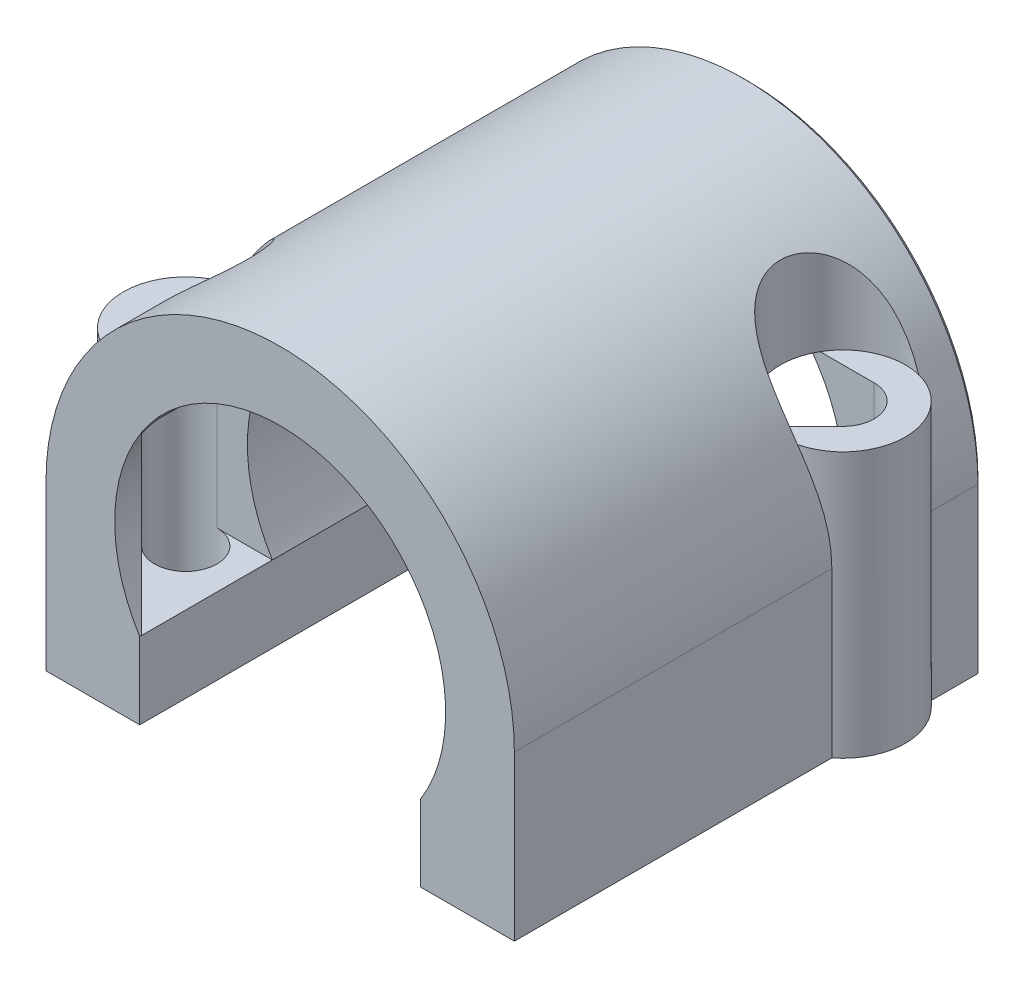
SolidWorks part; units mm, degrees
material "Custom Plastic"
ref_plane "Front Plane" through (0, 0, 0) normal (0, 0, 1) x (1, 0, 0)
ref_plane "Top Plane" through (0, 0, 0) normal (0, 1, 0) x (1, 0, 0)
ref_plane "Right Plane" through (0, 0, 0) normal (1, 0, 0) x (0, 0, -1)
sketch "Sketch1" plane through (0, 0, 0) normal (0, 0, 1) x (1, 0, 0)
  line L0 (-9, -10.5) -> (9, -10.5)
  line L1 (-9, -10.5) -> (-15, -10.5)
  line L2 (-15, -10.5) -> (15, -10.5) construction
  line L3 (-9, -5.4083) -> (-9, -10.5) construction
  line L4 (-15, 0) -> (-15, -10.5)
  line L5 (9, -5.4083) -> (9, -10.5) construction
  line L6 (9, -10.5) -> (15, -10.5)
  line L7 (15, -10.5) -> (15, 0)
  arc A1 (15, 0) -> (-15, 0) centre (0, 0) ccw
  circle A2 centre (0, 0) radius 10.5 construction
  dimension "D1" = 21
  dimension "D2" = 4.5
  dimension "D3" = 18
extrude "Boss-Extrude1" add sketch "Sketch1" along normal blind 30
sketch "Sketch4" plane through (0, -10.5, 0) normal (0, -1, 0) x (1, 0, 0)
  line L0 (0, 0) -> (0, 30) construction
  line L1 (-15, 30) -> (15, 30) construction
  line L2 (11, 29) -> (11, -1) construction
  line L4 (12.55, 6.5) -> (-12.55, 23.5) construction
  line L5 (-12.55, 27.5) -> (-12.55, 19.5)
  line L6 (12.55, 2.5) -> (12.55, 10.5)
  circle A0 centre (0, 15) radius 11 construction
  circle A1 centre (12.55, 6.5) radius 1.55 construction
  arc A2 (12.55, 2.5) -> (12.55, 10.5) centre (12.55, 6.5) ccw
  arc A3 (-12.55, 27.5) -> (-12.55, 19.5) centre (-12.55, 23.5) ccw
  dimension "D1" = 22
  dimension "D2" = 3.1
  dimension "D3" = 8
  dimension "D4" = 17
extrude "Boss-Extrude2" add sketch "Sketch4" against normal blind 17
sketch "Sketch2" plane through (0, -10.5, 0) normal (0, -1, 0) x (1, 0, 0)
  line L0 (10.9, 29) -> (10.9, -1) construction
  line L1 (0, 0) -> (0, 30) construction
  line L4 (12.55, 6.5) -> (-12.55, 23.5) construction
  circle A0 centre (12.55, 6.5) radius 1.65 construction
  arc A1 (-13.5185, 27.381) -> (-13.5185, 19.619) centre (-12.55, 23.5) ccw construction
  circle A2 centre (-12.55, 23.5) radius 1.65 construction
  circle A3 centre (12.55, 6.5) radius 2
  circle A4 centre (-12.55, 23.5) radius 2
  arc A6 (13.5185, 2.619) -> (13.5185, 10.381) centre (12.55, 6.5) ccw construction
  dimension "D1" = 3.3
  dimension "D4" = 4
extrude "Cut-Extrude7" cut sketch "Sketch2" against normal through all
sketch "Sketch3" plane through (0, -10.5, 0) normal (0, -1, 0) x (1, 0, 0)
  circle A0 centre (12.55, 6.5) radius 4
  arc A1 (12.55, 2.5) -> (12.55, 10.5) centre (12.55, 6.5) ccw construction
  arc A2 (-12.55, 27.5) -> (-12.55, 19.5) centre (-12.55, 23.5) ccw construction
  circle A3 centre (-12.55, 23.5) radius 4
  dimension "D1" = 8
extrude "Cut-Extrude2" cut sketch "Sketch3" against normal through all from offset 17 offset against normal yes
sketch "Sketch5" plane through (0, 0, 30) normal (0, 0, 1) x (1, 0, 0)
  line L1 (0, 0) -> (0, -10.5) construction
  line L2 (-11, -10.5) -> (11, -10.5) construction
  line L3 (-9, -10.5) -> (9, -10.5)
  line L4 (9, -10.5) -> (9, -5.6)
  line L5 (-9, -10.5) -> (-9, -5.6)
  arc A0 (9, -5.6) -> (-9, -5.6) centre (0, 0) ccw
  dimension "D1" = 10.6
  dimension "D2" = 18
extrude "Cut-Extrude3" cut sketch "Sketch5" against normal through all
sketch "Sketch6" plane through (0, 0, 0) normal (0, 1, 0) x (1, 0, 0)
  line L0 (0, 0) -> (0, -30) construction
  line L1 (0, -24.9142) -> (-13.9642, -24.9142) construction
  line L2 (0, -24.9142) -> (0, -21.5)
  line L3 (0, -21.5) -> (-12.55, -21.5)
  line L4 (-13.9642, -24.9142) -> (-12.55, -21.5)
  line L7 (0, -7.9142) -> (13.9642, -7.9142) construction
  line L8 (0, -7.9142) -> (0, -4.5)
  line L9 (0, -4.5) -> (12.55, -4.5)
  line L10 (13.9642, -7.9142) -> (12.55, -4.5)
  line L11 (0, -7.9142) -> (12.55, -4.5) construction
  line L12 (0, -4.5) -> (13.9642, -7.9142) construction
  line L30 (13.9642, -7.9142) -> (9, -12.8784)
  line L32 (9, -12.8784) -> (0, -7.9142)
  line L33 (-13.9642, -24.9142) -> (-9, -29.8784)
  line L35 (-9, -29.8784) -> (0, -24.9142)
  line L36 (-9, 0) -> (-9, -30) construction
  line L37 (9, 0) -> (9, -30) construction
  line L38 (12.55, -2.5) -> (12.55, -10.5) construction
  circle A2 centre (-12.55, -23.5) radius 2 construction
  circle A3 centre (12.55, -6.5) radius 2 construction
  point P0 (-6.275, -23.5)
  point P8 (6.9821, -6.5)
  dimension "D1" = 45
  dimension "D2" = 45
extrude "Cut-Extrude8" cut sketch "Sketch6" against normal up to vertex (5.6 mm away) and the other way up to vertex (6.5 mm away)
chamfer "Chamfer1" distance 0.3 angle 45 7 edges at (15, -5.25, 0) (0, 15, 0) (-15, -5.25, 0) (-12, -10.5, 0) (-9, -8.05, 0) (0, 10.6, 0) (9, -8.05, 0)
equation "\"y-cross-rib-thickness\"=6"
equation "\"y-rib-thickness\"=6"
equation "\"bed-plate-thickness\"=6"
equation "\"x-plate-thickness\"=5"
equation "\"rod-diameter\"=12"
equation "\"t-nut-hole-diameter\"=3"
equation "\"y-plate-thickness\"=5"
equation "\"enclosure-thickness\"=0.6"
equation "\"M3-Clearance\"=3.3"
equation "\"M4-Clearance\"=4.3"
equation "\"M5-Clearance\"=5.3"
equation "\"M6-Clearance\"=6.3"
equation "\"M8-Clearance\"=8.3"
equation "\"623-Bearing-Dia\"=11.2"
